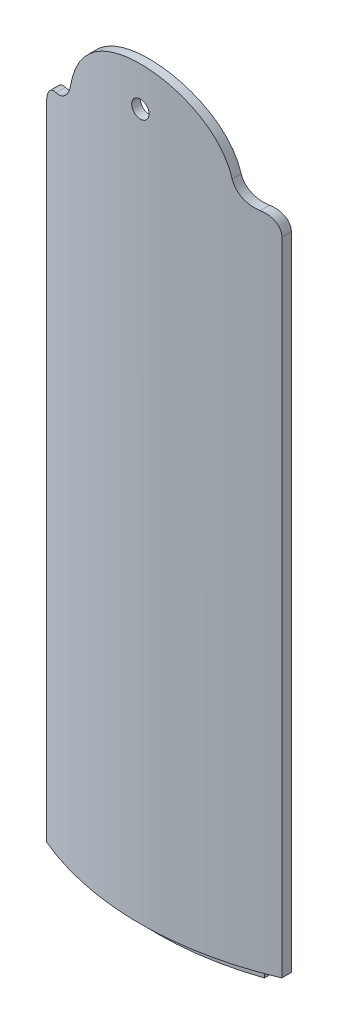
SolidWorks part; units mm, degrees
ref_plane "Спереди" through (0, 0, 0) normal (0, 0, 1) x (1, 0, 0)
ref_plane "Сверху" through (0, 0, 0) normal (0, 1, 0) x (1, 0, 0)
ref_plane "Справа" through (0, 0, 0) normal (1, 0, 0) x (0, 0, -1)
sketch "Эскиз1" plane through (0, 0, 0) normal (0, 1, 0) x (1, 0, 0)
  line L0 (-13.5, -1000.3895) -> (-13.5, 48999.6105) construction
  line L1 (13.5, -1000.9042) -> (13.5, 48999.0958) construction
  line L2 (10.5, -1012.3324) -> (10.5, 48987.6676) construction
  line L3 (-10.5, -1009.8614) -> (-10.5, 48990.1386) construction
  line L4 (-13.5, -30.6594) -> (-13.5, -31.749)
  line L5 (13.5, -30.6594) -> (13.5, -31.749)
  line L6 (-10.5, -30.7571) -> (-10.5, -31.8119)
  line L7 (10.5, -30.7571) -> (10.5, -31.8119)
  circle A0 centre (0, 0) radius 34.5 construction
  circle A1 centre (0, 0) radius 33.5 construction
  arc A2 (-13.5, -31.749) -> (13.5, -31.749) centre (0, 0) ccw
  arc A3 (-13.5, -30.6594) -> (-10.5, -31.8119) centre (0, 0) ccw
  arc A4 (10.5, -31.8119) -> (13.5, -30.6594) centre (0, 0) ccw
  circle A5 centre (0, 0) radius 32.5 construction
  arc A6 (-10.5, -30.7571) -> (10.5, -30.7571) centre (0, 0) ccw
extrude "Бобышка-Вытянуть1" add sketch "Эскиз1" along normal blind 76
sketch "Эскиз2" plane through (0, 0, 0) normal (0, -1, 0) x (1, 0, 0)
  line L0 (-10.5, 31.8119) -> (-10.5, 30.7571)
  line L1 (10.5, 31.8119) -> (10.5, 30.7571)
  line L2 (-10.5, 29.6985) -> (-10.5, 30.7571)
  line L3 (10.5, 29.6985) -> (10.5, 30.7571)
  arc A0 (-10.5, 31.8119) -> (10.5, 31.8119) centre (0, 0) ccw construction
  arc A1 (13.5, 30.6594) -> (10.5, 31.8119) centre (0, 0) ccw construction
  circle A3 centre (0, 0) radius 33.5 construction
  arc A4 (-10.5, 31.8119) -> (10.5, 31.8119) centre (0, 0) cw
  circle A5 centre (0, 0) radius 32.5 construction
  circle A6 centre (0, 0) radius 31.5 construction
  arc A7 (-10.5, 29.6985) -> (10.5, 29.6985) centre (0, 0) cw
extrude "Бобышка-Вытянуть2" add sketch "Эскиз2" along normal blind 2 and the other way blind 76
sketch "Эскиз3" plane through (0, 0, 0) normal (0, 0, 1) x (1, 0, 0)
  line L0 (13.5, 76) -> (-13.5, 76) construction
  line L3 (-29.777, 76) -> (-29.777, 102.2524)
  line L4 (-29.777, 102.2524) -> (31.5978, 102.2524)
  line L5 (31.5978, 102.2524) -> (31.5978, 75.7055)
  line L7 (-13.5, -924) -> (-13.5, 49076) construction
  line L8 (13.5, -924) -> (13.5, 49076) construction
  line L9 (-13.5, 73.6523) -> (-29.777, 73.6523)
  line L10 (-29.777, 73.6523) -> (-29.777, 76)
  line L11 (13.5, 73.6523) -> (31.5978, 73.6523)
  line L12 (31.5978, 73.6523) -> (31.5978, 75.7055)
  circle A0 centre (0, 76) radius 9.5 construction
  circle A3 centre (-12.2037, 78.7055) radius 3 construction
  circle A4 centre (12.2037, 78.7055) radius 3 construction
  arc A5 (-11.7212, 75.7445) -> (-9.2748, 78.0562) centre (-12.2037, 78.7055) ccw
  arc A6 (9.2748, 78.0562) -> (11.7212, 75.7445) centre (12.2037, 78.7055) ccw
  arc A7 (9.2748, 78.0562) -> (-9.2748, 78.0562) centre (0, 76) ccw
  circle A8 centre (-11.3802, 73.6523) radius 2.1198 construction
  circle A11 centre (11.3802, 73.6523) radius 2.1198 construction
  arc A12 (-11.7212, 75.7445) -> (-13.5, 73.6523) centre (-11.3802, 73.6523) ccw
  arc A13 (11.7212, 75.7445) -> (13.5, 73.6523) centre (11.3802, 73.6523) cw
sketch "Эскиз6" plane through (0, 76, 0) normal (0, 1, 0) x (1, 0, 0)
  line L0 (-10.5, -30.7571) -> (-10.5, -31.8119)
  line L1 (-13.5, -30.6594) -> (-13.5, -31.749)
  line L2 (10.5, -30.7571) -> (10.5, -31.8119)
  line L3 (13.5, -30.6594) -> (13.5, -31.749)
  arc A0 (-13.5, -31.749) -> (13.5, -31.749) centre (0, 0) ccw
  arc A1 (-10.5, -30.7571) -> (10.5, -30.7571) centre (0, 0) ccw
  arc A2 (-13.5, -30.6594) -> (-10.5, -31.8119) centre (0, 0) ccw
  arc A3 (10.5, -31.8119) -> (13.5, -30.6594) centre (0, 0) ccw
extrude "Бобышка-Вытянуть3" add sketch "Эскиз6" along normal blind 9.5
extrude "Вырез-Вытянуть1" cut sketch "Эскиз3" along normal blind 78.5
ref_plane "Плоскость4" through (0, 76, 0) normal (0, -1, 0) x (-1, 0, 0)
sketch "Эскиз7" plane through (0, 76, 0) normal (0, -1, 0) x (-1, 0, 0)
  line L0 (10.5, -30.7571) -> (10.5, -31.8119) construction
  line L1 (-10.5, -31.8119) -> (-10.5, -30.7571) construction
  line L5 (10.5, -29.6985) -> (10.5, -31.8119)
  line L6 (-10.5, -29.6985) -> (-10.5, -31.8119)
  arc A1 (10.5, -31.8119) -> (-10.5, -31.8119) centre (0, 0) ccw construction
  arc A2 (10.5, -31.8119) -> (11.7212, -31.3826) centre (0, 0) ccw construction
  circle A3 centre (0, 0) radius 33.5 construction
  arc A4 (10.5, -31.8119) -> (-10.5, -31.8119) centre (0, 0) cw
  arc A5 (10.5, -29.6985) -> (-10.5, -29.6985) centre (0, 0) cw
extrude "Вырез-Вытянуть2" cut sketch "Эскиз7" against normal blind 78.5 and the other way blind 4
sketch "Эскиз8" plane through (0, 0, 0) normal (0, 0, 1) x (1, 0, 0)
  line L0 (-1013.5, 76) -> (48986.5, 76) construction
  line L3 (-1004.6715, 81) -> (48995.3285, 81) construction
  circle A0 centre (0, 81) radius 1
extrude "Вырез-Вытянуть3" cut sketch "Эскиз8" along normal blind 46.5
sketch "Эскиз9" plane through (0, -2, 0) normal (0, -1, 0) x (1, 0, 0)
  line L0 (-10.5, 31.8119) -> (-10.5, 29.6985) construction
  line L1 (10.5, 29.6985) -> (10.5, 31.8119) construction
  line L2 (-10.5, 31.8119) -> (-10.5, 30.7552)
  line L3 (10.5, 31.8119) -> (10.5, 30.7552)
  arc A0 (-10.5, 31.8119) -> (10.5, 31.8119) centre (0, 0) cw
  arc A1 (-9.2748, 32.1905) -> (-11.7212, 31.3826) centre (0, 0) ccw construction
  arc A2 (13.5, 30.6594) -> (10.5, 31.8119) centre (0, 0) ccw construction
  circle A3 centre (0, 0) radius 31.5 construction
  circle A4 centre (0, 0) radius 32.5 construction
  arc A5 (-10.5, 30.7552) -> (10.5, 30.7552) centre (0, 0.0334) cw
extrude "Вырез-Вытянуть4" cut sketch "Эскиз9" against normal blind 2
